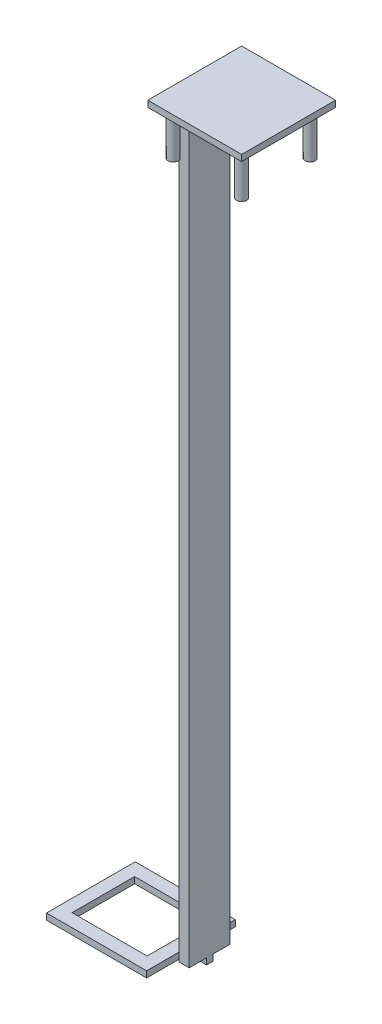
SolidWorks part; units mm, degrees
ref_plane "Front Plane" through (0, 0, 0) normal (0, 0, 1) x (1, 0, 0)
ref_plane "Top Plane" through (0, 0, 0) normal (0, 1, 0) x (1, 0, 0)
ref_plane "Right Plane" through (0, 0, 0) normal (1, 0, 0) x (0, 0, -1)
sketch "Sketch1" plane through (0, 0, 0) normal (0, 1, 0) x (1, 0, 0)
  line L0 (0.1397, 7.0235) -> (-0.8763, 7.0235)
  line L1 (0.1397, 1.3053) -> (-0.8763, 1.3053)
  line L2 (0.1397, 7.0235) -> (0.1397, 8.3288)
  line L3 (0.1397, 8.3288) -> (2.1717, 8.3288)
  line L4 (2.1717, 8.3288) -> (2.1717, 0)
  line L5 (2.1717, 0) -> (0.1397, 0)
  line L6 (0.1397, 0) -> (0.1397, 1.3053)
  line L7 (-0.8763, 1.3053) -> (-0.8763, 7.0235)
  dimension "D1" = 2.032
  dimension "D2" = 1.3053
  dimension "D3" = 8.3288
  dimension "D4" = 1.016
extrude "Boss-Extrude1" add sketch "Sketch1" along normal blind 152.4
sketch "Sketch2" plane through (0, 152.4, 0) normal (0, 1, 0) x (1, 0, 0)
  line L0 (-0.8763, 4.1644) -> (2.1717, 4.1644) construction
  line L1 (-0.8763, 13.6894) -> (18.1737, 13.6894)
  line L2 (-0.8763, 13.6894) -> (-0.8763, -5.3606)
  line L3 (-0.8763, -5.3606) -> (18.1737, -5.3606)
  line L4 (18.1737, 13.6894) -> (18.1737, -5.3606)
  line L5 (-0.8763, 7.0235) -> (-0.8763, 1.3053) construction
  line L6 (2.1717, 0) -> (2.1717, 8.3288) construction
  dimension "D1" = 19.05
  dimension "D2" = 19.05
extrude "Boss-Extrude2" add sketch "Sketch2" along normal blind 1.27
sketch "Sketch3" plane through (0, 152.4, 0) normal (0, -1, 0) x (1, 0, 0)
  line L0 (1.7732, -11.0399) -> (8.6487, -11.0399) construction
  line L1 (1.7732, -11.0399) -> (15.6028, 2.7897) construction
  line L3 (-0.8763, -4.1644) -> (18.1737, -4.1644) construction
  line L4 (-0.8763, -7.0235) -> (-0.8763, -1.3053) construction
  line L5 (18.1737, 5.3606) -> (18.1737, -13.6894) construction
  line L6 (8.6487, -13.6894) -> (8.6487, 5.3606) construction
  line L7 (18.1737, -13.6894) -> (-0.8763, -13.6894) construction
  line L8 (-0.8763, 5.3606) -> (18.1737, 5.3606) construction
  circle A0 centre (15.6028, 2.7897) radius 1.016
  circle A1 centre (15.6028, -11.1185) radius 1.016
  circle A2 centre (1.6946, -11.1185) radius 1.016
  circle A3 centre (1.6946, 2.7897) radius 1.016
  dimension "D3" = 2.032
  dimension "D1" = 45
  dimension "D2" = 19.558
extrude "Boss-Extrude3" add sketch "Sketch3" along normal blind 8.89
sketch "Sketch4" plane through (0, 0, 0) normal (0, -1, 0) x (1, 0, 0)
  line L0 (2.1717, -4.1644) -> (-0.8763, -4.1644) construction
  line L1 (-21.9583, 4.8356) -> (-1.6383, 4.8356)
  line L2 (-21.9583, 4.8356) -> (-21.9583, -13.1644)
  line L3 (-21.9583, -13.1644) -> (-1.6383, -13.1644)
  line L4 (-1.6383, 4.8356) -> (-1.6383, -3.5294)
  line L5 (2.1717, 0) -> (2.1717, -8.3288) construction
  line L6 (-0.8763, -7.0235) -> (-0.8763, -1.3053) construction
  line L7 (2.1717, -3.5294) -> (2.1717, -4.7994)
  line L8 (2.1717, -3.5294) -> (-1.6383, -3.5294)
  line L9 (2.1717, -4.7994) -> (-1.6383, -4.7994)
  line L10 (-0.8763, -4.1644) -> (-1.6383, -4.1644) construction
  line L11 (-1.6383, -4.7994) -> (-1.6383, -13.1644)
  dimension "D1" = 20.32
  dimension "D2" = 18
  dimension "D3" = 0.635
  dimension "D4" = 3.81
extrude "Boss-Extrude4" add sketch "Sketch4" along normal blind 1.27
sketch "Sketch5" plane through (0, 0, 0) normal (0, 1, 0) x (1, 0, 0)
  line L0 (-19.4183, 10.5144) -> (-4.1783, 10.5144)
  line L1 (-4.1783, 10.5144) -> (-4.1783, -2.1856)
  line L2 (-4.1783, -2.1856) -> (-19.4183, -2.1856)
  line L3 (-19.4183, -2.1856) -> (-19.4183, 10.5144)
  line L4 (-1.6383, 4.7994) -> (-1.6383, 3.5294) construction
  line L5 (-1.6383, 4.1644) -> (-4.1783, 4.1644) construction
  dimension "D1" = 15.24
  dimension "D2" = 12.7
  dimension "D3" = 2.54
extrude "Cut-Extrude1" cut sketch "Sketch5" against normal through all
